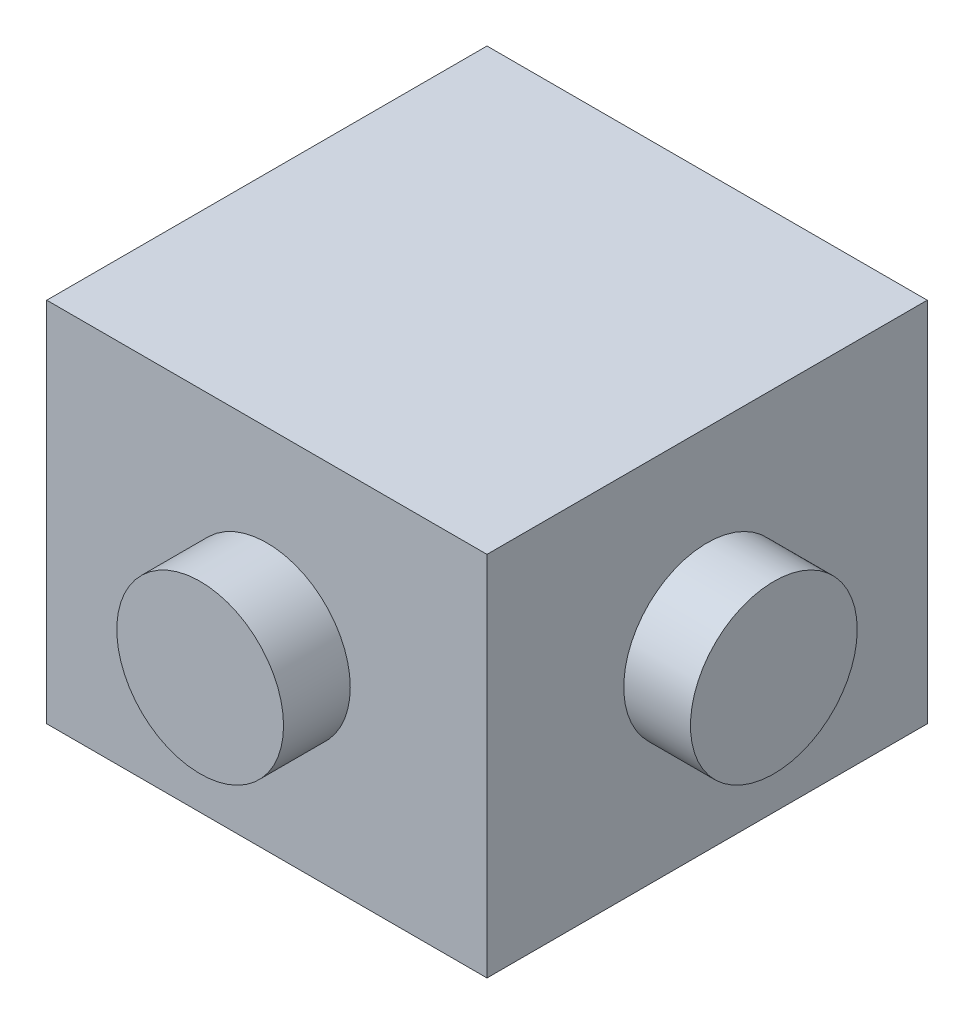
SolidWorks part; units mm, degrees
ref_plane "Front Plane" through (0, 0, 0) normal (0, 0, 1) x (1, 0, 0)
ref_plane "Top Plane" through (0, 0, 0) normal (0, 1, 0) x (1, 0, 0)
ref_plane "Right Plane" through (0, 0, 0) normal (1, 0, 0) x (0, 0, -1)
sketch "Sketch1" plane through (0, 0, 0) normal (0, 1, 0) x (1, 0, 0)
  line L1 (-8.382, -8.382) -> (8.382, -8.382)
  line L2 (-8.382, -8.382) -> (-8.382, 8.382)
  line L3 (-8.382, 8.382) -> (8.382, 8.382)
  line L4 (8.382, -8.382) -> (8.382, 8.382)
  line L5 (-8.382, -8.382) -> (8.382, 8.382) construction
  line L6 (-8.382, 8.382) -> (8.382, -8.382) construction
  point P0 (0, 0)
  dimension "D1" = 16.764
  dimension "D2" = 16.764
extrude "Boss-Extrude1" add sketch "Sketch1" along normal blind 13.97
sketch "Sketch2" plane through (0, 0, 8.382) normal (0, 0, 1) x (1, 0, 0)
  line L0 (-8.382, 13.97) -> (8.382, 13.97) construction
  line L1 (8.382, 13.97) -> (8.382, 0) construction
  circle A0 centre (0, 6.985) radius 3.175
  dimension "D1" = 6.35
  dimension "D2" = 6.985
  dimension "D3" = 8.382
extrude "Boss-Extrude2" add sketch "Sketch2" along normal blind 2.54
mirror "Mirror1" about plane through (0, 0, 0) normal (0, 0, 1) of "Boss-Extrude2"
sketch "Sketch3" plane through (8.382, 0, 0) normal (1, 0, 0) x (0, 0, -1)
  line L0 (8.382, 13.97) -> (8.382, 0) construction
  line L1 (-8.382, 13.97) -> (8.382, 13.97) construction
  circle A0 centre (0, 6.985) radius 3.175
  dimension "D1" = 6.35
  dimension "D2" = 8.382
  dimension "D3" = 6.985
extrude "Boss-Extrude3" add sketch "Sketch3" along normal blind 2.54
mirror "Mirror2" about plane through (0, 0, 0) normal (1, 0, 0) of "Boss-Extrude3"
